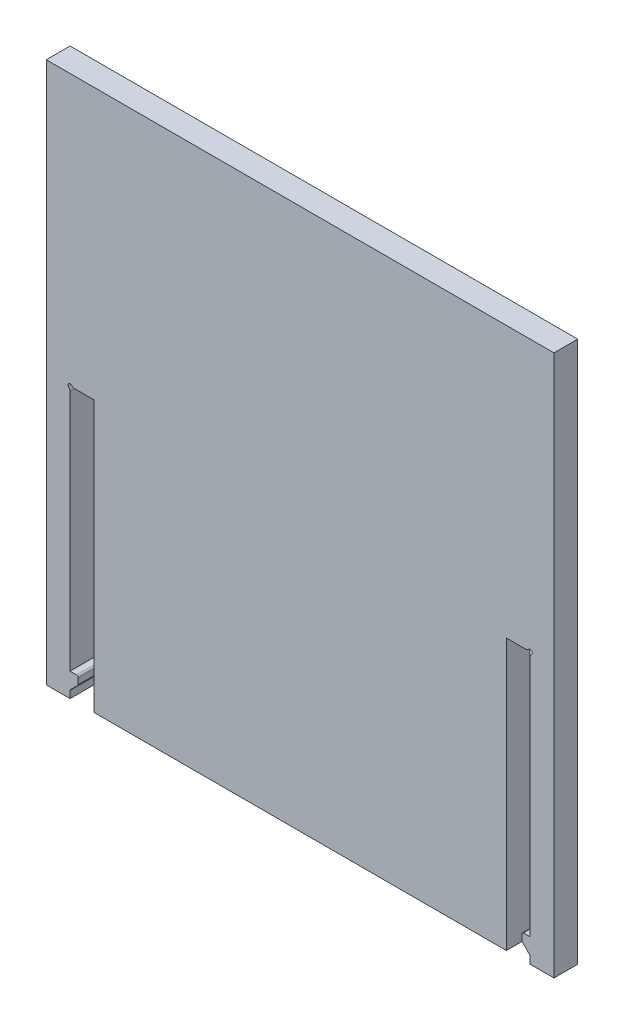
SolidWorks part; units mm, degrees
ref_plane "Front Plane" through (0, 0, 0) normal (0, 0, 1) x (1, 0, 0)
ref_plane "Top Plane" through (0, 0, 0) normal (0, 1, 0) x (1, 0, 0)
ref_plane "Right Plane" through (0, 0, 0) normal (1, 0, 0) x (0, 0, -1)
sketch "Sketch1" plane through (0, 0, 0) normal (0, 0, 1) x (1, 0, 0)
  line L1 (-31.26, 33.3375) -> (31.26, 33.3375)
  line L2 (-31.26, 33.3375) -> (-31.26, -33.3375)
  line L3 (-31.26, -33.3375) -> (31.26, -33.3375)
  line L4 (31.26, 33.3375) -> (31.26, -33.3375)
  line L5 (-31.26, 33.3375) -> (31.26, -33.3375) construction
  line L6 (-31.26, -33.3375) -> (31.26, 33.3375) construction
  point P0 (0, 0)
  dimension "D1" = 62.52
  dimension "D2" = 66.675
extrude "Boss-Extrude1" add sketch "Sketch1" along normal blind 2.93
sketch "Sketch2" plane through (0, 0, 2.93) normal (0, 0, 1) x (1, 0, 0)
  line L0 (-31.26, -33.3375) -> (31.26, -33.3375) construction
  line L1 (-28.33, -33.3375) -> (-25.4, -33.3375)
  line L2 (-28.33, -33.3375) -> (-28.33, 0)
  line L3 (-28.33, 0) -> (-25.4, 0)
  line L4 (-25.4, -33.3375) -> (-25.4, 0)
  line L5 (-31.26, 33.3375) -> (-31.26, -33.3375) construction
  dimension "D1" = 2.93
  dimension "D2" = 2.93
extrude "Cut-Extrude1" cut sketch "Sketch2" against normal through all
sketch "Sketch4" plane through (0, 0, 2.93) normal (0, 0, 1) x (1, 0, 0)
  line L0 (-28.33, 0) -> (-28.33, -33.3375) construction
  line L1 (-25.4, -33.3375) -> (-28.33, -33.3375) construction
  line L2 (-25.4, -33.3375) -> (-25.4, -30.4075) construction
  line L3 (-25.4, -30.4075) -> (-28.33, -30.4075) construction
  line L4 (-28.33, -33.3375) -> (-28.33, -30.4075) construction
  line L5 (-28.33, -30.4075) -> (-27.33, -30.4075)
  line L6 (-27.33, -30.4075) -> (-27.33, -31.4075)
  line L7 (-27.33, -31.4075) -> (-28.33, -32.4075)
  line L8 (-28.33, -32.4075) -> (-28.33, -30.4075)
  line M6 (-28.33, -33.3375) -> (-28.33, 0)
  dimension "D1" = 1
  dimension "D2" = 1
  dimension "D3" = 135
extrude "Boss-Extrude2" add sketch "Sketch4" against normal up to surface (2.93 mm away) contours L7 L6 L5 M6 up to face at (-13.4325, -8.3344, 0)
fillet "Fillet1" radius 0.2 3 edges at (-27.33, -31.4075, 1.465) (-28.33, -32.4075, 1.465) (-27.33, -30.4075, 1.465)
sketch "Sketch5" plane through (0, 0, 2.93) normal (0, 0, 1) x (1, 0, 0)
  circle A0 centre (-28.33, 0) radius 0.25
  dimension "D1" = 0.5
extrude "Cut-Extrude2" cut sketch "Sketch5" against normal through all
fillet "Fillet2" radius 0.5 2 edges at (-28.33, -0.25, 1.465) (-28.08, 0, 1.465)
mirror "Mirror1" about plane through (0, 0, 0) normal (1, 0, 0) of "Cut-Extrude1", "Boss-Extrude2", "Fillet2", "Cut-Extrude2", "Fillet1"
equation "\"thick\"= 2.93mm'Acrylic thickness"
equation "\"slot\"= 10mm'Slot width"
equation "\"D1@Sketch1\"=2+4 *\"thick\""
equation "\"D1@Boss-Extrude1\"=\"thick\""
equation "\"D1@Sketch2\"=\"thick\""
equation "\"D2@Sketch2\"=\"thick\""
